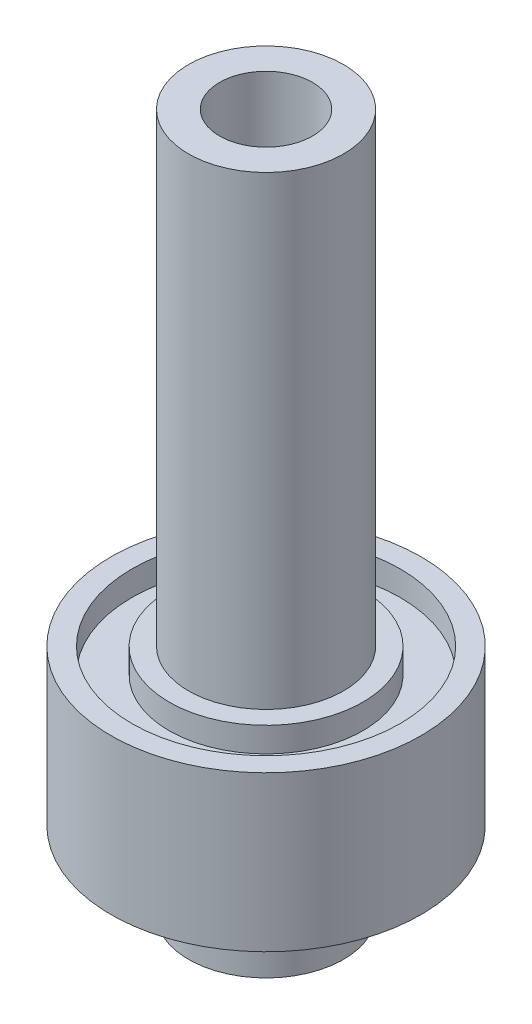
SolidWorks part; units mm, degrees
ref_plane "Front Plane" through (0, 0, 0) normal (0, 0, 1) x (1, 0, 0)
ref_plane "Top Plane" through (0, 0, 0) normal (0, 1, 0) x (1, 0, 0)
ref_plane "Right Plane" through (0, 0, 0) normal (1, 0, 0) x (0, 0, -1)
sketch "Sketch1" plane through (0, 0, 0) normal (0, 0, 1) x (1, 0, 0)
  line L0 (-3.81, 0) -> (-6.35, 0)
  line L1 (-6.35, 0) -> (-6.35, 6.35)
  line L2 (-6.35, 6.35) -> (-12.7, 6.35)
  line L3 (-12.7, 6.35) -> (-12.7, 19.05)
  line L4 (-12.7, 19.05) -> (-10.9855, 19.05)
  line L5 (-10.9855, 19.05) -> (-10.9855, 17.018)
  line L6 (-10.9855, 17.018) -> (-7.9375, 17.018)
  line L7 (-7.9375, 17.018) -> (-7.9375, 19.05)
  line L8 (-7.9375, 19.05) -> (-6.35, 19.05)
  line L9 (-6.35, 19.05) -> (-6.35, 57.15)
  line L10 (-6.35, 57.15) -> (-3.81, 57.15)
  line L13 (-3.81, 57.15) -> (-3.81, 0)
  line L14 (0, 0) -> (0, 38.457) construction
  point P14 (-3.81, 57.15)
  point P17 (-4.1658, 57.15)
  dimension "D1" = 3.81
  dimension "D2" = 6.35
  dimension "D3" = 3.048
  dimension "D4" = 2.032
  dimension "D5" = 1.5875
  dimension "D6" = 12.7
  dimension "D8" = 38.1
  dimension "D10" = 6.35
  dimension "D11" = 12.7
revolve "Revolve1" add sketch "Sketch1" angle 360 about L14
